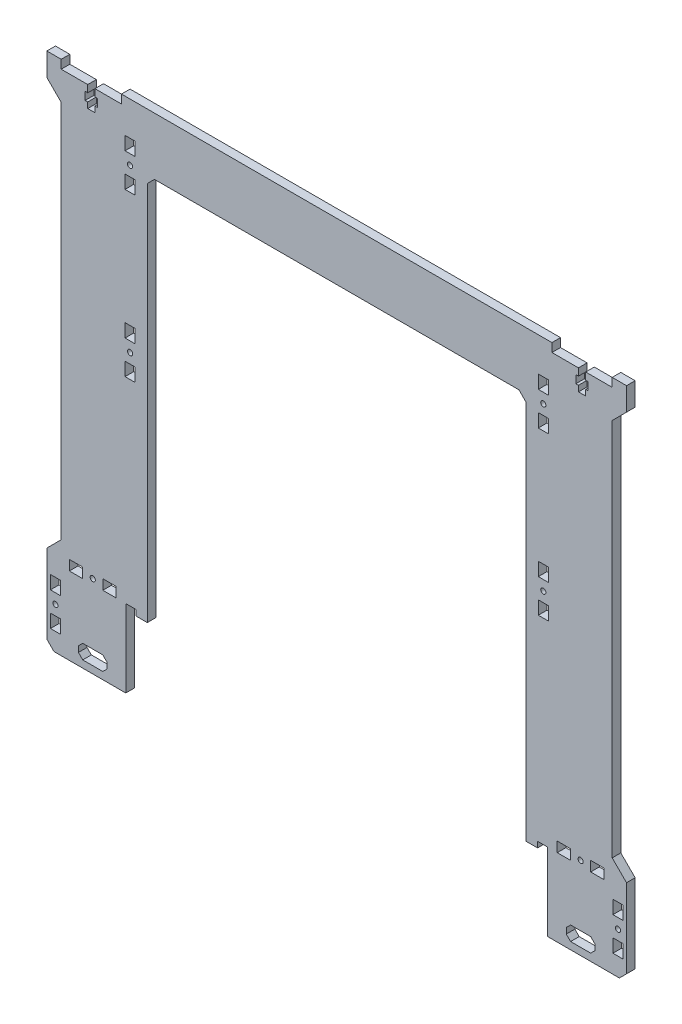
SolidWorks part; units mm, degrees
ref_plane "Plan de face" through (0, 0, 0) normal (0, 0, 1) x (1, 0, 0)
ref_plane "Plan de dessus" through (0, 0, 0) normal (0, 1, 0) x (1, 0, 0)
ref_plane "Plan de droite" through (0, 0, 0) normal (1, 0, 0) x (0, 0, -1)
sketch "Esquisse1" plane through (0, 0, 0) normal (0, 0, 1) x (1, 0, 0)
  line L0 (0, 0) -> (0, 40)
  line L1 (0, 40) -> (-150, 40)
  line L2 (-150, 40) -> (-150, 34)
  line L3 (-150, 34) -> (-192, 34)
  line L4 (-192, 34) -> (-192, 40)
  line L5 (-192, 40) -> (-202, 40)
  line L6 (-202, 40) -> (-202, 24)
  line L7 (-202, 24) -> (-192, 14)
  line L8 (-192, 14) -> (-192, -250)
  line L9 (-192, -250) -> (-202, -260)
  line L10 (-202, -260) -> (-202, -320)
  line L11 (-202, -320) -> (-147, -320)
  line L12 (-147, -320) -> (-147, -266)
  line L13 (-147, -266) -> (-140, -266)
  line L14 (-140, -266) -> (-140, -270)
  line L15 (-140, -270) -> (-132, -270)
  line L16 (-132, -270) -> (-132, 0)
  line L17 (-132, 0) -> (0, 0)
  line L19 (0, 0) -> (0, 40) construction
  line L20 (-202, 24) -> (-202, -260) construction
  dimension "D1" = 40
  dimension "D2" = 404
  dimension "D3" = 42
  dimension "D4" = 6
  dimension "D5" = 16
  dimension "D6" = 45
  dimension "D7" = 10
  dimension "D8" = 360
  dimension "D9" = 60
  dimension "D10" = 60
  dimension "D11" = 8
  dimension "D12" = 7
  dimension "D13" = 50
  dimension "D14" = 4
extrude "Boss.-Extru.1" add sketch "Esquisse1" along normal mid plane 6
sketch "Esquisse2" plane through (0, 0, 3) normal (0, 0, 1) x (1, 0, 0)
  line L0 (-144, 40) -> (-144, -266) construction
  line L1 (0, 40) -> (-150, 40) construction
  line L2 (-144, 0) -> (-132, 0) construction
  line L4 (-132, -270) -> (-132, 0) construction
  line L6 (-147, -266) -> (-140, -266) construction
  line L7 (-202, -260) -> (-202, -320) construction
  line L9 (-202, -320) -> (-147, -320) construction
  line L11 (-170, -262.5) -> (-170, -310) construction
  line L12 (-150, 34) -> (-192, 34) construction
  line B0 (-144, 16.3) -> (-144, 0) construction
  line B1 (-142.2, 0) -> (-145.8, 0) construction
  line B2 (-140.5, 16.3) -> (-140.5, 7)
  line B3 (-140.5, 16.3) -> (-147.5, 16.3)
  line B4 (-147.5, 16.3) -> (-147.5, 7)
  line B5 (-140.5, 7) -> (-147.5, 7)
  line B6 (-140.5, 16.3) -> (-147.5, 7) construction
  line B7 (-147.5, 16.3) -> (-140.5, 7) construction
  line B8 (-147.5, -16.3) -> (-140.5, -7) construction
  line B9 (-140.5, -16.3) -> (-147.5, -7) construction
  line B10 (-140.5, -7) -> (-147.5, -7)
  line B11 (-147.5, -16.3) -> (-147.5, -7)
  line B12 (-140.5, -16.3) -> (-147.5, -16.3)
  line B13 (-140.5, -16.3) -> (-140.5, -7)
  circle B14 centre (-144, 0) radius 1.8
  line B15 (-144, -96.7) -> (-144, -113) construction
  line B16 (-142.2, -113) -> (-145.8, -113) construction
  line B17 (-140.5, -96.7) -> (-140.5, -106)
  line B18 (-140.5, -96.7) -> (-147.5, -96.7)
  line B19 (-147.5, -96.7) -> (-147.5, -106)
  line B20 (-140.5, -106) -> (-147.5, -106)
  line B21 (-140.5, -96.7) -> (-147.5, -106) construction
  line B22 (-147.5, -96.7) -> (-140.5, -106) construction
  line B23 (-147.5, -129.3) -> (-140.5, -120) construction
  line B24 (-140.5, -129.3) -> (-147.5, -120) construction
  line B25 (-140.5, -120) -> (-147.5, -120)
  line B26 (-147.5, -129.3) -> (-147.5, -120)
  line B27 (-140.5, -129.3) -> (-147.5, -129.3)
  line B28 (-140.5, -129.3) -> (-140.5, -120)
  circle B29 centre (-144, -113) radius 1.8
  line B30 (-186.3, -262.5) -> (-170, -262.5) construction
  line B31 (-170, -260.7) -> (-170, -264.3) construction
  line B32 (-186.3, -259) -> (-177, -259)
  line B33 (-186.3, -259) -> (-186.3, -266)
  line B34 (-186.3, -266) -> (-177, -266)
  line B35 (-177, -259) -> (-177, -266)
  line B36 (-186.3, -259) -> (-177, -266) construction
  line B37 (-186.3, -266) -> (-177, -259) construction
  line B38 (-153.7, -266) -> (-163, -259) construction
  line B39 (-153.7, -259) -> (-163, -266) construction
  line B40 (-163, -259) -> (-163, -266)
  line B41 (-153.7, -266) -> (-163, -266)
  line B42 (-153.7, -259) -> (-153.7, -266)
  line B43 (-153.7, -259) -> (-163, -259)
  circle B44 centre (-170, -262.5) radius 1.8
  line B45 (-196, -307.3) -> (-196, -291) construction
  line B46 (-197.8, -291) -> (-194.2, -291) construction
  line B47 (-199.5, -307.3) -> (-199.5, -298)
  line B48 (-199.5, -307.3) -> (-192.5, -307.3)
  line B49 (-192.5, -307.3) -> (-192.5, -298)
  line B50 (-199.5, -298) -> (-192.5, -298)
  line B51 (-199.5, -307.3) -> (-192.5, -298) construction
  line B52 (-192.5, -307.3) -> (-199.5, -298) construction
  line B53 (-192.5, -274.7) -> (-199.5, -284) construction
  line B54 (-199.5, -274.7) -> (-192.5, -284) construction
  line B55 (-199.5, -284) -> (-192.5, -284)
  line B56 (-192.5, -274.7) -> (-192.5, -284)
  line B57 (-199.5, -274.7) -> (-192.5, -274.7)
  line B58 (-199.5, -274.7) -> (-199.5, -284)
  circle B59 centre (-196, -291) radius 1.8
  line B60 (-180, -308) -> (-177, -305)
  line B61 (-177, -315) -> (-163, -315)
  line B62 (-180, -312) -> (-180, -308)
  line B63 (-177, -305) -> (-163, -305)
  line B64 (-160, -312) -> (-160, -308)
  line B65 (-180, -315) -> (-160, -305) construction
  line B66 (-180, -305) -> (-160, -315) construction
  line B67 (-163, -305) -> (-160, -308)
  line B68 (-163, -315) -> (-160, -312)
  line B69 (-180, -312) -> (-177, -315)
  line B70 (-186.5, 34) -> (-186.5, 39)
  line B71 (-185.5, 40) -> (-179.5, 40)
  line B72 (-178.5, 39) -> (-178.5, 34)
  line B73 (-178.5, 34) -> (-173.5, 34)
  line B74 (-173.5, 34) -> (-173.5, 29)
  line B75 (-173.5, 29) -> (-175.3, 29)
  line B76 (-175.3, 29) -> (-175.3, 23.5)
  line B77 (-175.3, 23.5) -> (-173.5, 23.5)
  line B78 (-173.5, 23.5) -> (-173.5, 19.5)
  line B79 (-173.5, 19.5) -> (-168.5, 19.5)
  line B80 (-171, 19.5) -> (-171, 34) construction
  line B81 (-155.5, 34) -> (-163.5, 34)
  line B82 (-178.5, 34) -> (-186.5, 34)
  line B83 (-168.5, 23.5) -> (-168.5, 19.5)
  line B84 (-166.7, 23.5) -> (-168.5, 23.5)
  line B85 (-166.7, 29) -> (-166.7, 23.5)
  line B86 (-168.5, 29) -> (-166.7, 29)
  line B87 (-168.5, 34) -> (-168.5, 29)
  line B88 (-163.5, 34) -> (-168.5, 34)
  line B89 (-163.5, 39) -> (-163.5, 34)
  line B90 (-156.5, 40) -> (-162.5, 40)
  line B91 (-155.5, 34) -> (-155.5, 39)
  line B92 (-173.5, 34) -> (-168.5, 34)
  arc B93 (-179.5, 40) -> (-178.5, 39) centre (-179.5, 39) cw
  arc B94 (-186.5, 39) -> (-185.5, 40) centre (-185.5, 39) cw
  arc B95 (-155.5, 39) -> (-156.5, 40) centre (-156.5, 39) ccw
  arc B96 (-162.5, 40) -> (-163.5, 39) centre (-162.5, 39) ccw
  line M5 (-150, 34) -> (-192, 34)
  dimension "D1" = 12
  dimension "D2" = 32
  dimension "D3" = 31
  dimension "D4" = 6
  dimension "D5" = 10
sketch_block_instance "attache_femelle-1"
sketch_block "attache_femelle" parameters "D1"=3.6, "D2"=9.3, "D3"=7, "D4"=7
sketch_block_instance "attache_femelle-2"
sketch_block_instance "attache_femelle-3"
sketch_block_instance "attache_femelle-4"
sketch_block_instance "cable_hole-1"
sketch_block "cable_hole" parameters "D1"=20, "D2"=10
sketch_block_instance "attache_male-1"
sketch_block "attache_male" parameters "D7"=1, "D1"=5, "D2"=5, "D3"=5.5, "D4"=1.8, "D5"=4, "D6"=2.5
extrude "Enlèv. mat.-Extru.1" cut sketch "Esquisse2" against normal up to next contours B5 B2 B3 B4 | B12 B13 B10 B11 | B20 B17 B18 B19 | B29 | B14 | B87 B74 B75 B76 B77 B78 B79 B83 B84 B85 B86 M5 | B27 B28 B25 B26 | B42 B43 B40 B41 | B44 | B35 B32 B33 B34 | B57 B58 B55 B56 | B59 | B50 B47 B48 B49 | B62 B69 B61 B68 B64 B67 B63 B60
chamfer "Chanfrein1" distance 5 angle 45 2 edges at (-202, -320, 0) (-132, 0, 0)
mirror "Symétrie1" about plane through (0, 0, 3) normal (-1, 0, 0) of bodies 102
equation "\"W\"= \"W@Prusa i4.2.sldasm\""
equation "\"D2@Esquisse1\"=\"W\"+104"
equation "\"H\"= \"H@Prusa i4.2.sldasm\""
equation "\"D8@Esquisse1\"=\"H\""
